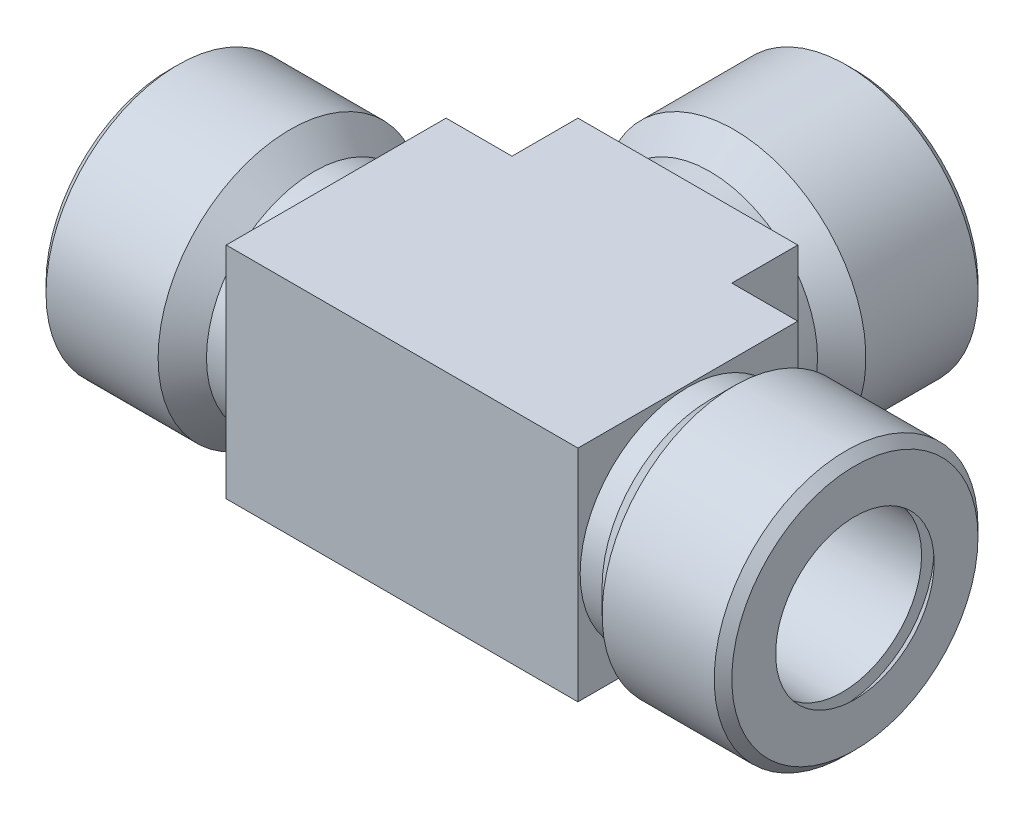
SolidWorks part; units mm, degrees
ref_plane "Front Plane" through (0, 0, 0) normal (0, 0, 1) x (1, 0, 0)
ref_plane "Top Plane" through (0, 0, 0) normal (0, 1, 0) x (1, 0, 0)
ref_plane "Right Plane" through (0, 0, 0) normal (1, 0, 0) x (0, 0, -1)
ref_plane "Plane1" through (0, 12.7, 0) normal (0, 1, 0) x (-1, 0, 0)
sketch "Sketch1" plane through (0, 12.7, 0) normal (0, 1, 0) x (-1, 0, 0)
  line L0 (-59.944, 12.7) -> (-59.944, -20.32)
  line L1 (-59.944, -20.32) -> (-19.304, -20.32)
  line L2 (-19.304, -20.32) -> (-19.304, 12.7)
  line L3 (-19.304, 12.7) -> (-59.944, 12.7)
extrude "Boss-Extrude1" add sketch "Sketch1" against normal blind 25.4
sketch "Sketch2" plane through (0, -12.7, 0) normal (0, -1, 0) x (1, 0, 0)
  line L0 (52.324, -12.7) -> (52.324, -20.32)
  line L1 (52.324, -20.32) -> (59.944, -20.32)
  line L2 (59.944, -20.32) -> (59.944, -12.7)
  line L3 (59.944, -12.7) -> (52.324, -12.7)
extrude "Cut-Extrude1" cut sketch "Sketch2" against normal through all
sketch "Sketch3" plane through (0, -12.7, 0) normal (0, -1, 0) x (1, 0, 0)
  line L0 (26.924, -20.32) -> (26.924, -12.7)
  line L1 (26.924, -12.7) -> (19.304, -12.7)
  line L2 (19.304, -12.7) -> (19.304, -20.32)
  line L3 (19.304, -20.32) -> (26.924, -20.32)
extrude "Cut-Extrude2" cut sketch "Sketch3" against normal through all
sketch "Sketch4" plane through (19.304, 0, 0) normal (-1, 0, 0) x (0, 0, 1)
  circle A0 centre (0, 0) radius 12.446
extrude "Boss-Extrude2" add sketch "Sketch4" along normal blind 2.54
sketch "Sketch5" plane through (16.764, 0, 0) normal (-1, 0, 0) x (0, 0, 1)
  circle A0 centre (0, 0) radius 12.446
extrude "Boss-Extrude3" add sketch "Sketch5" along normal blind 2.794 draft 45 draft outward yes
sketch "Sketch6" plane through (13.97, 0, 0) normal (-1, 0, 0) x (0, 0, 1)
  circle A0 centre (0, 0) radius 15.24
extrude "Boss-Extrude4" add sketch "Sketch6" along normal blind 13.97
sketch "Sketch7" plane through (59.944, 0, 0) normal (1, 0, 0) x (0, 0, -1)
  circle A0 centre (0, 0) radius 12.446
extrude "Boss-Extrude5" add sketch "Sketch7" along normal blind 2.54
sketch "Sketch8" plane through (62.484, 0, 0) normal (1, 0, 0) x (0, 0, -1)
  circle A0 centre (0, 0) radius 12.446
extrude "Boss-Extrude6" add sketch "Sketch8" along normal blind 2.794 draft 45 draft outward yes
sketch "Sketch9" plane through (65.278, 0, 0) normal (1, 0, 0) x (0, 0, -1)
  circle A0 centre (0, 0) radius 15.24
extrude "Boss-Extrude7" add sketch "Sketch9" along normal blind 13.97
sketch "Sketch10" plane through (0, 0, -20.32) normal (0, 0, -1) x (-1, 0, 0)
  circle A0 centre (-39.624, 0) radius 12.446
extrude "Boss-Extrude8" add sketch "Sketch10" along normal blind 2.54
sketch "Sketch11" plane through (0, 0, -22.86) normal (0, 0, -1) x (-1, 0, 0)
  circle A0 centre (-39.624, 0) radius 12.446
extrude "Boss-Extrude9" add sketch "Sketch11" along normal blind 2.794 draft 45 draft outward yes
sketch "Sketch12" plane through (0, 0, -25.654) normal (0, 0, -1) x (-1, 0, 0)
  circle A0 centre (-39.624, 0) radius 15.24
extrude "Boss-Extrude10" add sketch "Sketch12" along normal blind 13.97
ref_plane "Plane2" through (13.5712, 0, 0) normal (-1, 0, 0) x (0, -1, 0)
sketch "Sketch13" plane through (13.5712, 0, 0) normal (-1, 0, 0) x (0, -1, 0)
  circle A0 centre (0, 0) radius 9.271
extrude "Cut-Extrude3" cut sketch "Sketch13" against normal blind 52.1056
ref_plane "Plane3" through (0, 0, -26.0528) normal (0, 0, -1) x (-1, 0, 0)
sketch "Sketch14" plane through (0, 0, -26.0528) normal (0, 0, -1) x (-1, 0, 0)
  circle A0 centre (-39.624, 0) radius 9.271
extrude "Cut-Extrude4" cut sketch "Sketch14" against normal up to next
sketch "Sketch15" plane through (0, 0, -39.624) normal (0, 0, -1) x (-1, 0, 0)
  circle A0 centre (-39.624, 0) radius 10.6117
extrude "Cut-Extrude5" cut sketch "Sketch15" against normal blind 1.4514 draft 45
sketch "Sketch16" plane through (0, 0, -26.0528) normal (0, 0, 1) x (1, 0, 0)
  circle A0 centre (39.624, 0) radius 8.8494
extrude "Cut-Extrude6" cut sketch "Sketch16" against normal blind 12.1199 draft 1.47 draft outward yes
sketch "Sketch17" plane through (0, 0, 0) normal (-1, 0, 0) x (0, 0, 1)
  circle A0 centre (0, 0) radius 10.6117
extrude "Cut-Extrude7" cut sketch "Sketch17" against normal blind 1.4514 draft 45
sketch "Sketch18" plane through (13.5712, 0, 0) normal (1, 0, 0) x (0, 0, -1)
  circle A0 centre (0, 0) radius 8.8494
extrude "Cut-Extrude8" cut sketch "Sketch18" against normal blind 12.1199 draft 1.47 draft outward yes
hole_wizard "Hole1" positions "Sketch20" profile "Sketch19" legacy
sketch "Sketch20" plane through (79.248, 0, 0) normal (1, 0, 0) x (0, 0, -1)
  point P0 (0, 0)
sketch "Sketch19" plane through (79.248, 0, 0) normal (0, 1, 0) x (0, 0, -1)
  line L0 (0, 0) -> (0, 1.4514)
  line L1 (0, 1.4514) -> (10.6117, 1.4514)
  line L2 (10.6117, 1.4514) -> (9.1604, 0)
  line L3 (9.1604, 0) -> (0, 0)
  line L4 (0, 110) -> (0, -10) construction
  dimension "Minor Diameter" = 21.2235
  dimension "Depth" = 1.4514
  dimension "Major Diameter" = 18.3208
sketch "Sketch21" plane through (65.6768, 0, 0) normal (-1, 0, 0) x (0, 0, 1)
  circle A0 centre (0, 0) radius 8.8494
extrude "Cut-Extrude9" cut sketch "Sketch21" against normal blind 12.1199 draft 1.47 draft outward yes
chamfer "Chamfer1" distance 1.016 angle 45 1 edges at (0, 0, 15.24)
chamfer "Chamfer2" distance 1.016 angle 45 1 edges at (79.248, 0, -15.24)
chamfer "Chamfer3" distance 1.016 angle 45 1 edges at (24.384, 0, -39.624)
